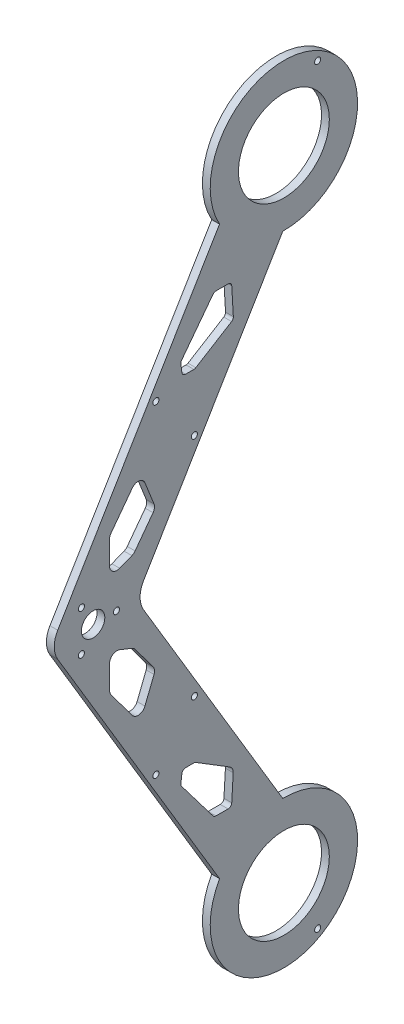
SolidWorks part; units mm, degrees
ref_plane "Front Plane" through (0, 0, 0) normal (1, 0, 0) x (0, 1, 0)
ref_plane "Top Plane" through (0, 0, 0) normal (0, 0, 1) x (0, 1, 0)
ref_plane "Right Plane" through (0, 0, 0) normal (0, 1, 0) x (-1, 0, 0)
sketch "sketch" plane through (0, 0, 0) normal (1, 0, 0) x (0, 1, 0)
  line L0 (260, 0) -> (-260, 0) construction
  line L1 (0, 0) -> (0, 280) construction
  line L2 (0, 280) -> (0, 197.29) construction
  line L3 (0, 197.29) -> (260, 0) construction
  line L4 (0, 197.29) -> (-260, 0) construction
  line L5 (0, 0) -> (130, 98.645) construction
  line L6 (130, 98.645) -> (130, 119.61) construction
  line L7 (130, 98.645) -> (130, 77.68) construction
  line L8 (130, 77.68) -> (0, 0) construction
  line L9 (130, 77.68) -> (260, 0) construction
  circle A0 centre (0, 0) radius 65 construction
  circle A1 centre (260, 0) radius 65 construction
  circle A2 centre (-260, 0) radius 65 construction
  point P4 (0, 0)
  dimension "D1" = 130
  dimension "D2" = 130
  dimension "D4" = 130
  dimension "D5" = 280
  dimension "D3" = 260
  dimension "D6" = 82.71
  dimension "D7" = 20.965
  dimension "D8" = 20.965
sketch "bogie base" plane through (0, 0, 0) normal (1, 0, 0) x (0, 1, 0)
  line L1 (260, 0) -> (-260, 0) construction
  line L3 (-25.7527, -15.3882) -> (9.8719, 5.8988) construction
  line L15 (285.7527, -15.3882) -> (234.2473, 15.3882) construction
  line L16 (130, 77.68) -> (260, 0) construction
  line L25 (124.8706, 92.0889) -> (14.6084, 26.203)
  line L26 (124.8706, 57.1411) -> (29.9966, 0.4502)
  line L27 (135.1294, 57.1411) -> (230.0034, 0.4502)
  line L28 (135.1294, 92.0889) -> (245.3916, 26.203)
  circle A0 centre (260, 0) radius 11.5 construction
  circle A1 centre (0, 0) radius 11.5 construction
  arc A2 (124.8706, 57.1411) -> (135.1294, 57.1411) centre (130, 48.5569) cw
  arc A3 (124.8706, 92.0889) -> (135.1294, 92.0889) centre (130, 83.5046) cw
  arc A8 (14.6084, 26.203) -> (29.9966, 0.4502) centre (0, 0) ccw
  arc A9 (230.0034, 0.4502) -> (245.3916, 26.203) centre (260, 0) ccw
  point P4 (130, 98.645)
  point P12 (0, 0)
  point P14 (-25.7527, -15.3882)
  point P18 (260, 0)
  point P19 (0, 0)
  point P24 (130, 98.645)
  point P26 (260, 0)
  point P29 (285.7527, -15.3882)
  point P33 (130, 60.2061)
  point P35 (130, 77.68)
  point P37 (130, 95.1539)
  point P38 (130, 77.68)
  point P41 (130, 98.645)
  point P43 (293.4468, -2.5119)
  point P46 (278.0586, -28.2646)
  point P49 (-18.0586, -28.2646)
  point P52 (-33.4468, -2.5119)
  dimension "D11" = 23
  dimension "D12" = 118.28
  dimension "D2" = 23
  dimension "D14" = 10
  dimension "D15" = 10
  dimension "D16" = 15
  dimension "D17" = 60
  dimension "D3" = 30
  dimension "D8" = 29.1231
  dimension "D18" = 5.8246
  dimension "D4" = 30
  dimension "D5" = 110.5211
  dimension "D6" = 15
  dimension "D7" = 30
  dimension "D9" = 190.4034
  dimension "D10" = 34.9478
  dimension "D13" = 241.72
extrude "extrude-base" add sketch "bogie base" along normal blind 3.18
sketch "Sketch4" plane through (0, 0, 0) normal (1, 0, 0) x (0, 1, 0)
  circle A0 centre (260, 0) radius 18.5
  circle A1 centre (0, 0) radius 18.5
  dimension "D1" = 37
  dimension "D2" = 37
extrude "Cut-motor holes\\" cut sketch "Sketch4" along normal blind 3.18
sketch "Sketch6" plane through (0, 0, 0) normal (1, 0, 0) x (0, 1, 0)
  line L0 (130, 82.445) -> (130, 66.92) construction
  line L2 (-25.7527, -15.3882) -> (-23.0229, -13.7571) construction
  line L3 (-25.7527, -15.3882) -> (9.8719, 5.8988) construction
  line L5 (-30.717, -0.8807) -> (-15.3288, -26.6334) construction
  line L6 (124.8706, 57.1411) -> (29.9966, 0.4502) construction
  line L7 (-25.3312, -9.8942) -> (-20.7147, -17.62) construction
  line L10 (106.8543, 81.3234) -> (122.2425, 55.5707) construction
  line L12 (-23.0229, -13.7571) -> (18.1814, 10.8641) construction
  line L13 (130, 77.68) -> (0, 0) construction
  line L14 (130, 77.68) -> (18.1814, 10.8641) construction
  line L15 (66.3966, 57.1484) -> (81.7848, 31.3957) construction
  line L16 (10.4873, 23.7405) -> (25.8755, -2.0123) construction
  line L17 (77.9536, 46.5803) -> (70.2278, 41.9638) construction
  line L18 (62.5337, 54.8402) -> (77.9219, 29.0875) construction
  line L19 (70.2595, 59.4566) -> (85.6477, 33.7039) construction
  line L20 (62.5337, 54.8402) -> (64.1648, 52.1104) construction
  line L21 (130, 77.68) -> (130, 68.17) construction
  line L22 (130, 68.17) -> (121.7723, 82.4492) construction
  line L23 (121.7723, 82.4492) -> (138.2488, 82.437) construction
  line L24 (138.2488, 82.437) -> (130, 68.17) construction
  line L25 (130, 77.68) -> (121.7723, 82.4492) construction
  circle A19 centre (64.1648, 52.1104) radius 1.25
  circle A22 centre (84.0166, 36.4337) radius 1.25
  circle A23 centre (130, 77.68) radius 4.765
  circle A24 centre (130, 68.17) radius 1.25
  circle A25 centre (121.7723, 82.4492) radius 1.25
  circle A26 centre (138.2488, 82.437) radius 1.25
  circle A27 centre (175.9834, 36.4337) radius 1.25
  circle A29 centre (195.8352, 52.1104) radius 1.25
  circle A33 centre (-23.0229, -13.7571) radius 1.25
  circle A34 centre (283.0229, -13.7571) radius 1.25
  point P12 (-23.0229, -13.7571)
  point P15 (-23.0229, -13.7571)
  point P25 (114.5484, 68.4471)
  point P32 (74.0907, 44.272)
  point P35 (18.1814, 10.8641)
  point P38 (74.0907, 44.272)
  point P41 (70.2278, 41.9638)
  point P44 (77.9536, 46.5803)
  dimension "D4" = 2.5
  dimension "D5" = 18
  dimension "D8" = 48
  dimension "D9" = 30
  dimension "D10" = 4.5
  dimension "D3" = 9
  dimension "D11" = 2.5
  dimension "D13" = 9.53
  dimension "D14" = 2.5
  dimension "D20" = 2.5
  dimension "D21" = 2.5
  dimension "D22" = 19.6131
  dimension "D23" = 30
  dimension "D24" = 26.82
  dimension "D25" = 2.5
  dimension "D26" = 25.2952
  dimension "D6" = 30
  dimension "D7" = 30.86
  dimension "D12" = 3.18
  dimension "D15" = 9.51
  dimension "D16" = 16.48
  dimension "D17" = 16.4764
  dimension "D18" = 16.48
  dimension "D19" = 9.51
  dimension "D27" = 3.18
extrude "support holes" cut sketch "Sketch6" along normal blind 3.18
sketch "Sketch7" plane through (0, 0, 0) normal (1, 0, 0) x (0, 1, 0)
  line L8 (130, 77.68) -> (0, 0) construction
  line L10 (54.884, 41.6464) -> (38.0344, 28.8608)
  line L11 (0, 0) -> (130, 98.645) construction
  line L12 (37.4411, 27.6659) -> (37.4411, 22.7346)
  line L13 (38.8533, 21.2372) -> (49.1659, 20.6321)
  line L14 (51.8962, 22.054) -> (60.3984, 35.8618)
  line L15 (60.6211, 36.6482) -> (60.6211, 40.0362)
  line L16 (59.3068, 41.5246) -> (55.9763, 41.9399)
  line L23 (130, 93.5046) -> (130, 58.5569) construction
  line L30 (200.6932, 41.5246) -> (204.0237, 41.9399)
  line L31 (199.3789, 36.6482) -> (199.3789, 40.0362)
  line L32 (208.5739, 21.2905) -> (199.6016, 35.8618)
  line L33 (221.1467, 21.2372) -> (209.939, 20.5796)
  line L34 (222.5589, 27.6659) -> (222.5589, 22.7346)
  line L35 (205.116, 41.6464) -> (221.9656, 28.8608)
  line L45 (112.8431, 70.9677) -> (103.2904, 70.9677)
  line L46 (101.4974, 70.3729) -> (89.955, 61.7684)
  line L47 (90.6414, 56.5748) -> (99.9403, 52.8845)
  line L48 (102.8399, 53.2677) -> (112.6629, 60.5904)
  line L49 (113.6584, 61.889) -> (115.6315, 66.8611)
  line L50 (146.3416, 61.889) -> (144.3685, 66.8611)
  line L51 (157.1601, 53.2677) -> (147.3371, 60.5904)
  line L52 (169.3586, 56.5748) -> (160.0597, 52.8845)
  line L53 (158.5026, 70.3729) -> (170.045, 61.7684)
  line L54 (147.1569, 70.9677) -> (156.7096, 70.9677)
  arc A9 (37.4411, 22.7346) -> (38.8533, 21.2372) centre (38.9411, 22.7346) ccw
  arc A10 (38.0344, 28.8608) -> (37.4411, 27.6659) centre (38.9411, 27.6659) ccw
  arc A12 (60.3984, 35.8618) -> (60.6211, 36.6482) centre (59.1211, 36.6482) ccw
  arc A13 (60.6211, 40.0362) -> (59.3068, 41.5246) centre (59.1211, 40.0362) ccw
  arc A14 (55.9763, 41.9399) -> (54.884, 41.6464) centre (55.7907, 40.4515) ccw
  arc A21 (135.1294, 92.0889) -> (124.8706, 92.0889) centre (130, 83.5046) ccw construction
  arc A22 (135.1294, 57.1411) -> (124.8706, 57.1411) centre (130, 48.5569) ccw construction
  arc A29 (204.0237, 41.9399) -> (205.116, 41.6464) centre (204.2093, 40.4515) cw
  arc A30 (199.3789, 40.0362) -> (200.6932, 41.5246) centre (200.8789, 40.0362) cw
  arc A31 (199.6016, 35.8618) -> (199.3789, 36.6482) centre (200.8789, 36.6482) cw
  arc A32 (209.939, 20.5796) -> (208.5739, 21.2905) centre (209.8512, 22.077) cw
  arc A33 (221.9656, 28.8608) -> (222.5589, 27.6659) centre (221.0589, 27.6659) cw
  arc A34 (222.5589, 22.7346) -> (221.1467, 21.2372) centre (221.0589, 22.7346) cw
  arc A44 (51.8962, 22.054) -> (49.1659, 20.6321) centre (49.3417, 23.6269) cw
  arc A45 (99.9403, 52.8845) -> (102.8399, 53.2677) centre (101.0469, 55.6729) ccw
  arc A46 (89.955, 61.7684) -> (90.6414, 56.5748) centre (91.748, 59.3632) ccw
  arc A47 (103.2904, 70.9677) -> (101.4974, 70.3729) centre (103.2904, 67.9677) ccw
  arc A48 (112.6629, 60.5904) -> (113.6584, 61.889) centre (110.8699, 62.9956) ccw
  arc A49 (115.6315, 66.8611) -> (112.8431, 70.9677) centre (112.8431, 67.9677) ccw
  arc A50 (144.3685, 66.8611) -> (147.1569, 70.9677) centre (147.1569, 67.9677) cw
  arc A51 (147.3371, 60.5904) -> (146.3416, 61.889) centre (149.1301, 62.9956) cw
  arc A52 (156.7096, 70.9677) -> (158.5026, 70.3729) centre (156.7096, 67.9677) cw
  arc A53 (170.045, 61.7684) -> (169.3586, 56.5748) centre (168.252, 59.3632) cw
  arc A54 (160.0597, 52.8845) -> (157.1601, 53.2677) centre (158.9531, 55.6729) cw
  point P48 (37.4411, 28.4106)
  point P53 (60.6211, 36.2235)
  point P58 (55.3704, 42.0155)
  point P144 (204.6296, 42.0155)
  point P145 (199.3789, 36.2235)
  point P146 (222.5589, 28.4106)
  dimension "D1" = 3
  dimension "D2" = 9.5527
  dimension "D3" = 1.5
  dimension "D4" = 14.3967
  dimension "D5" = 3
  dimension "D6" = 10.0044
  dimension "D7" = 12.2521
  dimension "D8" = 5.3492
extrude "Cut-lightening holes" cut sketch "Sketch7" along normal blind 3.18
